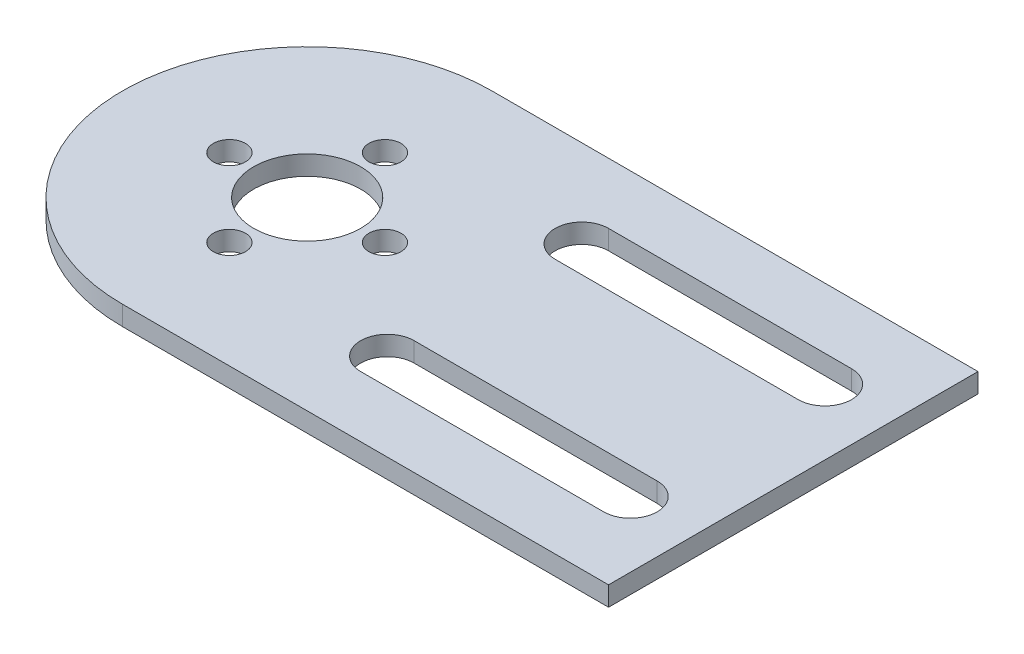
SolidWorks part; units mm, degrees
ref_plane "前视基准面" through (0, 0, 0) normal (0, 0, 1) x (1, 0, 0)
ref_plane "上视基准面" through (0, 0, 0) normal (0, 1, 0) x (1, 0, 0)
ref_plane "右视基准面" through (0, 0, 0) normal (1, 0, 0) x (0, 0, -1)
sketch "草图1" plane through (0, 0, 0) normal (0, 1, 0) x (1, 0, 0)
  line L0 (0, 19) -> (50, 19)
  line L1 (50, 19) -> (50, -19)
  line L2 (50, -19) -> (0, -19)
  arc A0 (0, 19) -> (0, -19) centre (0, 0) ccw
  dimension "D1" = 38
  dimension "D2" = 50
extrude "凸台-拉伸1" add sketch "草图1" along normal blind 2
sketch "草图2" plane through (0, 2, 0) normal (0, 1, 0) x (1, 0, 0)
  line L0 (0, 0) -> (25.3202, 0) construction
  line L1 (0, 0) -> (0, -16.4738) construction
  line L2 (18.25, 12.75) -> (43.25, 12.75)
  line L3 (43.25, 7.25) -> (18.25, 7.25)
  line L4 (43.25, -7.25) -> (18.25, -7.25)
  line L5 (18.25, -12.75) -> (43.25, -12.75)
  line L6 (50, -19) -> (50, 19) construction
  circle A0 centre (0, 0) radius 5.5
  circle A1 centre (0, -8) radius 1.65
  arc A5 (18.25, 12.75) -> (18.25, 7.25) centre (18.25, 10) ccw
  arc A6 (43.25, 7.25) -> (43.25, 12.75) centre (43.25, 10) ccw
  circle A7 centre (0, 0) radius 8 construction
  circle A8 centre (-8, 0) radius 1.65
  circle A9 centre (0, 8) radius 1.65
  circle A10 centre (8, 0) radius 1.65
  arc A11 (18.25, -12.75) -> (18.25, -7.25) centre (18.25, -10) cw
  arc A12 (43.25, -7.25) -> (43.25, -12.75) centre (43.25, -10) cw
  point P23 (0, 0)
  point P31 (46, 10)
  dimension "D1" = 11
  dimension "D2" = 16
  dimension "D3" = 3.3
  dimension "D5" = 5.5
  dimension "D6" = 5.5
  dimension "D7" = 10
  dimension "D8" = 10
  dimension "D9" = 4
  dimension "D10" = 25
  dimension "D4" = 4
extrude "切除-拉伸1" cut sketch "草图2" against normal through all
